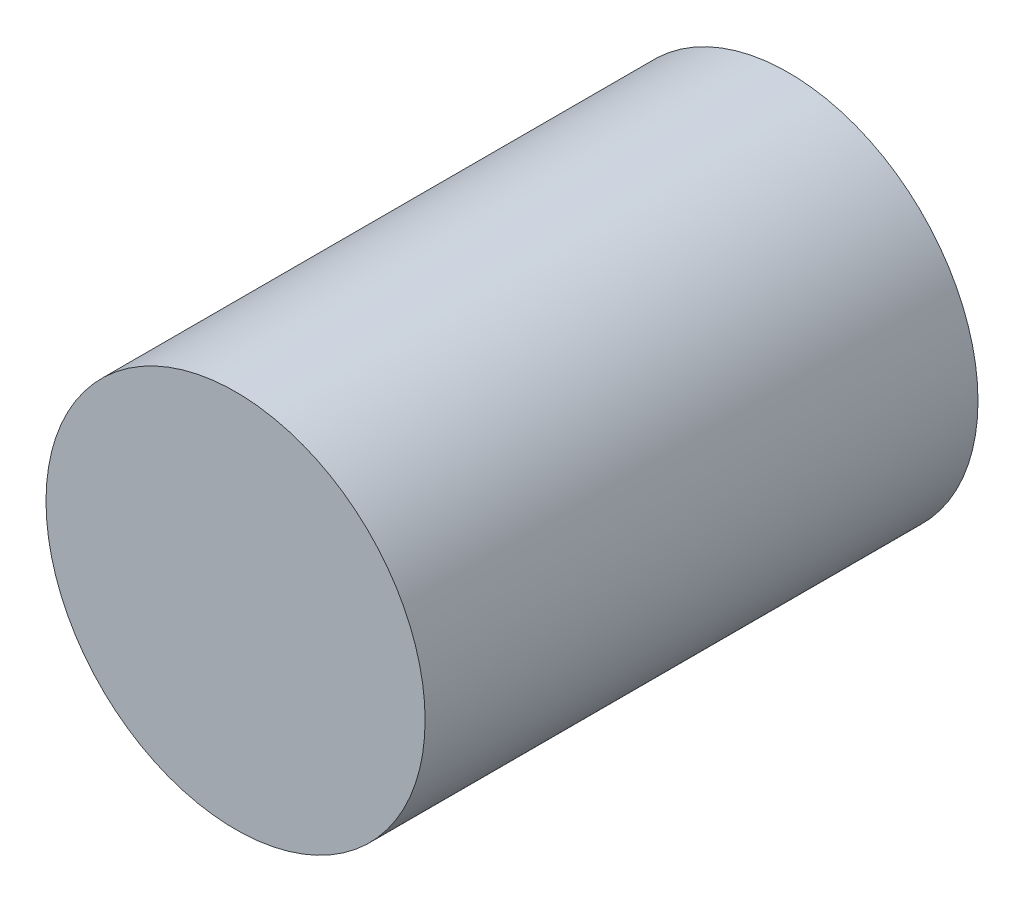
SolidWorks part; units mm, degrees
ref_plane "Front Plane" through (0, 0, 0) normal (0, 0, 1) x (1, 0, 0)
ref_plane "Top Plane" through (0, 0, 0) normal (0, 1, 0) x (1, 0, 0)
ref_plane "Right Plane" through (0, 0, 0) normal (1, 0, 0) x (0, 0, -1)
sketch "Sketch1" plane through (0, 0, 0) normal (0, 0, 1) x (1, 0, 0)
  circle A0 centre (0, 0) radius 17.399
  dimension "D1" = 34.798
extrude "Extrude1" add sketch "Sketch1" along normal blind 50.7492
